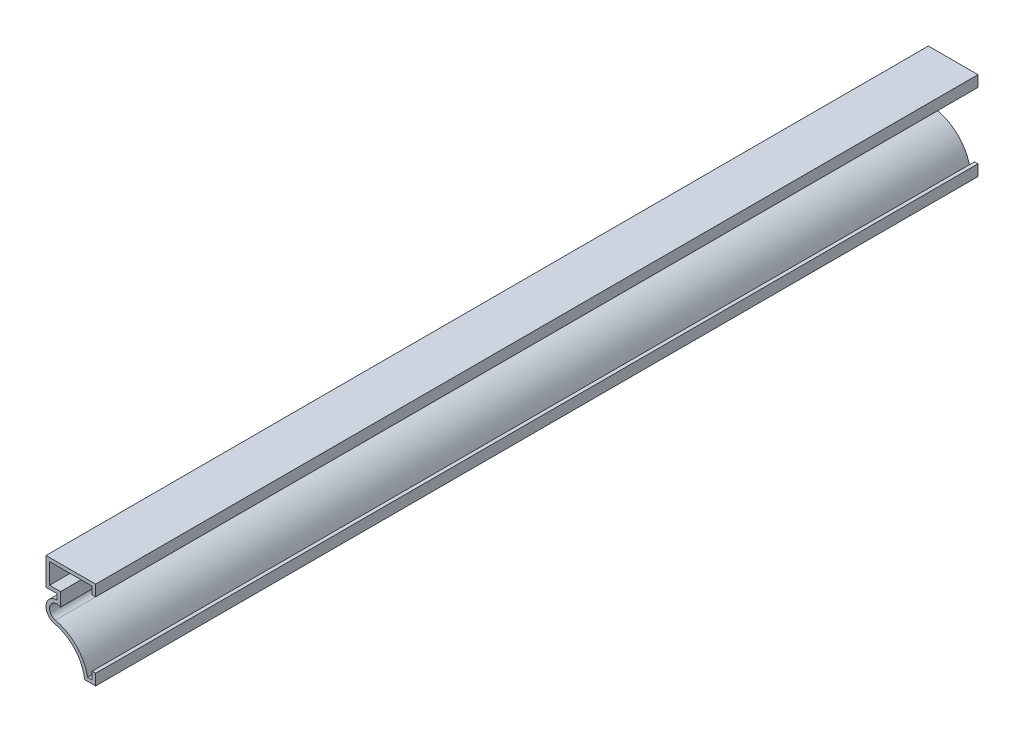
SolidWorks part; units mm, degrees
ref_plane "Front Plane" through (0, 0, 0) normal (0, 0, 1) x (1, 0, 0)
ref_plane "Top Plane" through (0, 0, 0) normal (0, 1, 0) x (1, 0, 0)
ref_plane "Right Plane" through (0, 0, 0) normal (1, 0, 0) x (0, 0, -1)
sketch "Sketch1" plane through (0, 0, 0) normal (0, 0, 1) x (1, 0, 0)
  line L0 (0, 0) -> (0, 25.4) construction
  line L1 (0, 22.225) -> (0, 25.4)
  line L2 (0, 25.4) -> (-14.2875, 25.4)
  line L3 (-14.2875, 25.4) -> (-14.2875, 17.4625)
  line L4 (-14.2875, 17.4625) -> (-11.1125, 17.4625)
  line L5 (-11.1125, 17.4625) -> (-11.1125, 15.875)
  line L6 (0, 3.175) -> (0, 0)
  line L7 (0, 0) -> (-3.175, 0)
  arc A0 (-11.1125, 15.875) -> (-11.8143, 9.6035) centre (-11.1125, 12.7) ccw
  arc A1 (-11.8143, 9.6035) -> (-3.175, 0) centre (-14.2875, -1.3091) cw
  point P13 (0, 0)
  point P14 (-3.6326, 0)
  point P15 (-12.5262, -0.5453)
  point P16 (-7.175, 9.3874)
  point P17 (0, 0)
  point P18 (-14.2875, -1.453)
  point P19 (-9.9368, 8.1096)
  point P20 (-9.9759, 15.0617)
  point P21 (-12.2451, 9.1813)
  point P22 (-2.8058, 0)
  point P23 (-11.737, 9.587)
  point P24 (-3.0406, 0)
  point P25 (-3.1825, 0)
  point P26 (0, 0)
  dimension "D1" = 25.4
  dimension "D2" = 14.2875
  dimension "D3" = 7.9375
  dimension "D4" = 1.5875
  dimension "D5" = 15.875
  dimension "D6" = 3.175
  dimension "D7" = 19.05
  dimension "D8" = 3.175
  dimension "D9" = 3.175
extrude "Extrude-Thin1" add sketch "Sketch1" against normal blind 254 thin thin type one direction wall 1.016
